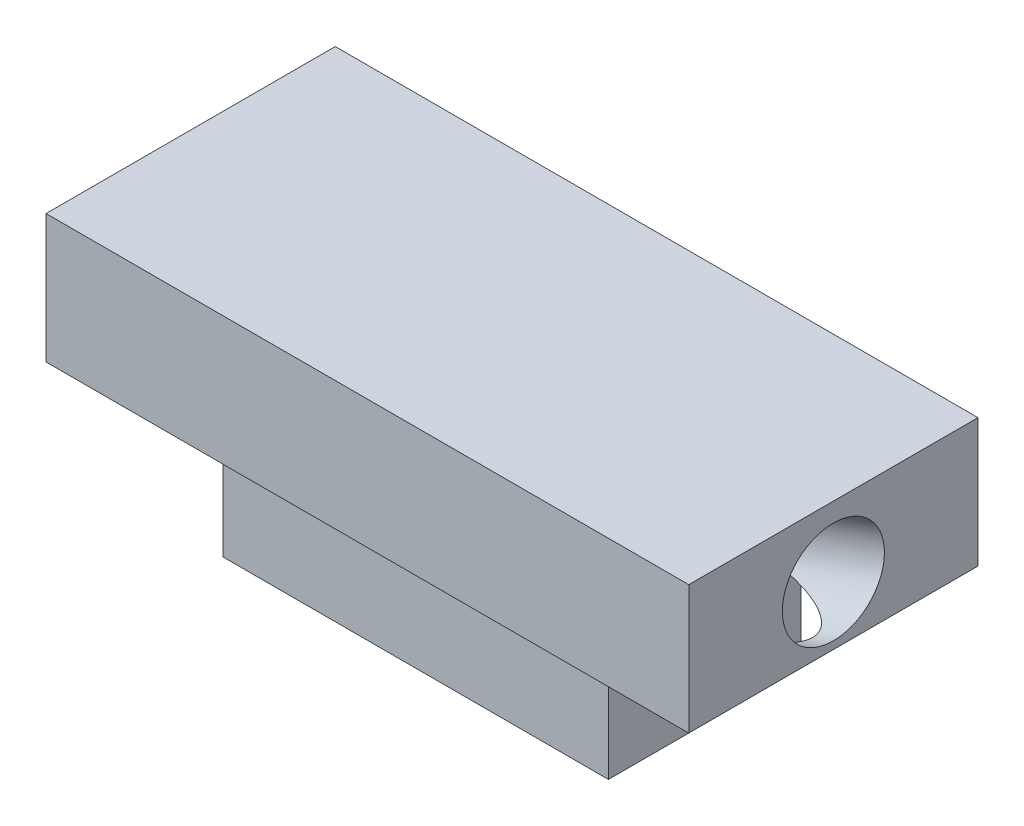
SolidWorks part; units mm, degrees
ref_plane "Front Plane" through (0, 0, 0) normal (0, 0, 1) x (1, 0, 0)
ref_plane "Top Plane" through (0, 0, 0) normal (0, 1, 0) x (1, 0, 0)
ref_plane "Right Plane" through (0, 0, 0) normal (1, 0, 0) x (0, 0, -1)
sketch "Sketch1" plane through (0, 0, 0) normal (0, 1, 0) x (1, 0, 0)
  line L1 (-1.0372, 1.1516) -> (1.9628, 1.1516)
  line L2 (-1.0372, -0.3484) -> (1.9628, -0.3484)
  line L3 (-1.0372, -0.3484) -> (-1.0372, 1.1516)
  line L4 (1.9628, 1.1516) -> (1.9628, -0.3484)
  dimension "D1" = 1.5
  dimension "D2" = 3
extrude "Boss-Extrude1" add sketch "Sketch1" along normal blind 1
sketch "Sketch2" plane through (0, 0, 0) normal (0, 0, 1) x (1, 0, 0)
  line L0 (-1.0372, 1) -> (-1.0372, 0) construction
  line L4 (-1.0372, 0) -> (4.7521, 2.1071)
  dimension "D1" = 70
ref_plane "Plane1" [suppressed] through (-1.3856, 1, 0) normal (-1, 0, 0) x (0, 0, 1)
sketch "Sketch5" plane through (0, 1, 0) normal (0, 1, 0) x (1, 0, 0)
  line L0 (0.4628, -0.3484) -> (0.4628, -0.7234) construction
  line L1 (-2.0372, 1.5266) -> (2.9628, 1.5266)
  line L2 (-2.0372, 1.5266) -> (-2.0372, -0.7234)
  line L3 (-2.0372, -0.7234) -> (2.9628, -0.7234)
  line L4 (2.9628, 1.5266) -> (2.9628, -0.7234)
  line L5 (-1.0372, 0.4016) -> (-2.0372, 0.4016) construction
  line L6 (-1.0372, -0.3484) -> (-1.0372, 1.1516) construction
  line L8 (-1.0372, -0.3484) -> (1.9628, -0.3484) construction
  dimension "D1" = 2.25
  dimension "D2" = 5
extrude "Boss-Extrude2" add sketch "Sketch5" along normal blind 1
sketch "Sketch4" plane through (-1.0372, 1, 0) normal (-1, 0, 0) x (0, 0, 1)
  line L0 (0.3484, -1) -> (-1.1516, -1) construction
  circle A0 centre (-0.4016, -1) radius 0.3969
  point P3 (-0.4016, -1)
  dimension "D1" = 0.7937
sweep "Cut-Sweep3" cut profiles "Sketch4" path "Sketch2"
